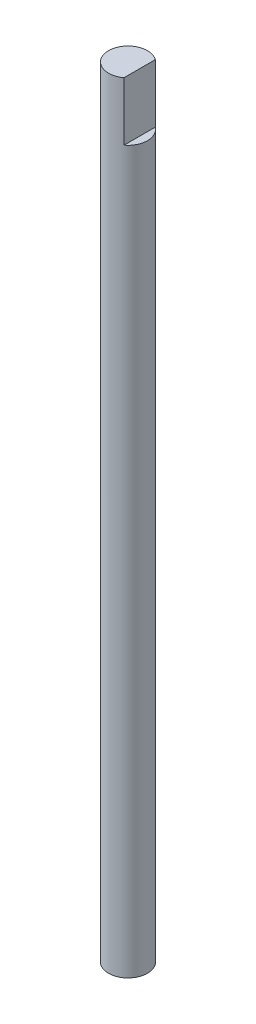
SolidWorks part; units mm, degrees
material "Chrome Stainless Steel"
ref_plane "Front Plane" through (0, 0, 0) normal (0, 0, 1) x (1, 0, 0)
ref_plane "Top Plane" through (0, 0, 0) normal (0, 1, 0) x (1, 0, 0)
ref_plane "Right Plane" through (0, 0, 0) normal (1, 0, 0) x (0, 0, -1)
sketch "Sketch1" plane through (0, 0, 0) normal (0, 1, 0) x (1, 0, 0)
  circle A0 centre (0, 0) radius 5
  dimension "D1" = 10
extrude "Rod" add sketch "Sketch1" along normal blind 200
sketch "Sketch2" plane through (0, 0, 0) normal (0, 0, 1) x (1, 0, 0)
  line L0 (5, 0) -> (5, 200) construction
  line L1 (3, 201.135) -> (5, 201.135)
  line L2 (3, 201.135) -> (3, 185)
  line L3 (3, 185) -> (5, 185)
  line L4 (5, 201.135) -> (5, 185)
  line L5 (5, 200) -> (-5, 200) construction
  line L6 (-5, 200) -> (-5, 0) construction
  dimension "D1" = 15
  dimension "D2" = 8
extrude "Slot" cut sketch "Sketch2" against normal through all both and the other way through all
equation "\"D2@Sketch2\"=\"D1@Sketch1\"-2"
